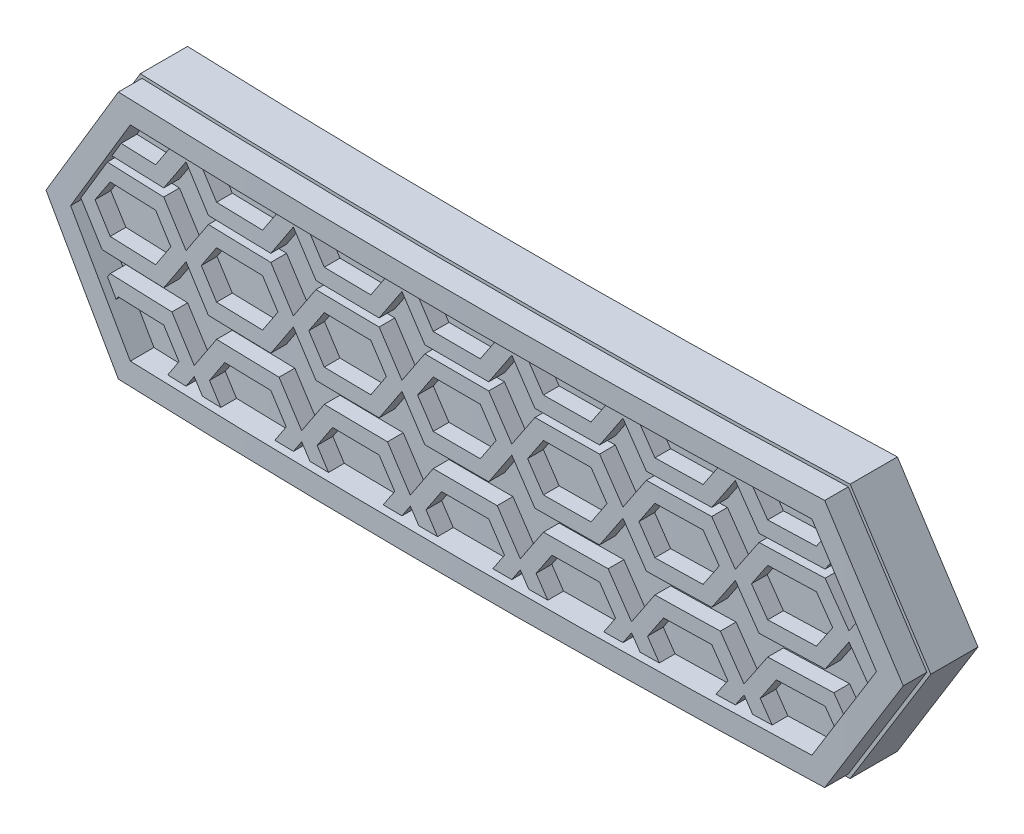
SolidWorks part; units mm, degrees
ref_plane "Front Plane" through (0, 0, 0) normal (0, 0, 1) x (1, 0, 0)
ref_plane "Top Plane" through (0, 0, 0) normal (0, 1, 0) x (1, 0, 0)
ref_plane "Right Plane" through (0, 0, 0) normal (1, 0, 0) x (0, 0, -1)
sketch "Sketch2" plane through (0, 0, 0) normal (0, 1, 0) x (1, 0, 0)
  line L3 (-73.1153, 2.6297) -> (-72.7519, 5.6076)
  line L4 (73.8847, 2.6297) -> (73.5213, 5.6076)
  arc A0 (-73.1153, 2.6297) -> (73.8847, 2.6297) centre (0.3847, 604.9793) ccw
  arc A1 (-72.7519, 5.6076) -> (73.5213, 5.6076) centre (0.3847, 604.9793) ccw
  dimension "D2" = 147
  dimension "D1" = 3
extrude "Boss-Extrude1" add sketch "Sketch2" along normal blind 25
sketch "Sketch3" plane through (0, 0, 0) normal (0, 0, 1) x (1, 0, 0)
  line L0 (0.3847, 25) -> (0, 0) construction
  line L1 (73.8847, 25) -> (-73.1153, 25) construction
  line L2 (-27.5937, 12.7392) -> (-22.6709, 20.843)
  line L3 (-22.6709, 20.843) -> (22.4834, 20.843)
  line L4 (-22.6709, 4.6354) -> (22.4834, 4.6354)
  line L5 (-27.5937, 12.7392) -> (-22.6709, 4.6354)
  line L6 (27.4063, 12.7392) -> (22.4834, 4.6354)
  line L7 (27.4063, 12.7392) -> (22.4834, 20.843)
  line L12 (-73.1153, 0) -> (73.8847, 0)
  line L13 (73.8847, 0) -> (73.8847, 25)
  line L14 (73.8847, 25) -> (-73.1153, 25)
  line L15 (-73.1153, 25) -> (-73.1153, 0)
  line L16 (-73.1153, 0) -> (73.8847, 0)
  line L17 (73.8847, 0) -> (73.8847, 25)
  line L18 (73.8847, 25) -> (-73.1153, 25)
  line L19 (-73.1153, 25) -> (-73.1153, 0)
  point P10 (-0.0937, 4.6354)
  point P12 (-0.0937, 20.843)
  dimension "D1" = 55
  dimension "D2" = 0
extrude "Cut-Extrude1" cut sketch "Sketch3" against normal through all both and the other way through all
sketch "Sketch4" plane through (0, 0, 0) normal (0, 0, 1) x (1, 0, 0)
  line L0 (-18.8894, 14.093) -> (-18.8894, 12.6877) construction
  line L1 (-25.6228, 13.0876) -> (-25.625, 13.0908)
  line L2 (8.1082, 6.1354) -> (9.31, 6.1354)
  line L3 (-17.4817, 6.1354) -> (-16.2798, 6.1354)
  line L4 (-12.8918, 6.1354) -> (-11.69, 6.1354)
  line L6 (-25.3906, 12.7392) -> (24.8112, 12.7392) construction
  line L7 (-18.8894, 23.6403) -> (-18.8894, 18.1877) construction
  line L10 (-10.4817, 6.1354) -> (-9.2798, 6.1354)
  line L11 (2.5774, 18.8928) -> (2.5774, 18.8879)
  line L12 (25.6512, 12.7392) -> (21.6395, 19.343)
  line L13 (21.6395, 19.343) -> (-21.827, 19.343)
  line L14 (-21.827, 19.343) -> (-25.8386, 12.7392)
  line L15 (-25.8386, 12.7392) -> (-21.827, 6.1354)
  line L16 (-21.827, 6.1354) -> (21.6395, 6.1354)
  line L17 (21.6395, 6.1354) -> (25.6512, 12.7392)
  line L18 (24.8368, 14.0798) -> (24.2638, 15.0231)
  line L19 (17.6789, 19.343) -> (16.4771, 19.343)
  line L20 (-23.0132, 17.3903) -> (-23.6207, 16.3903)
  line L21 (-23.8612, 9.4841) -> (-23.2882, 8.5408)
  line L22 (-19.8918, 6.1354) -> (-18.69, 6.1354)
  line L23 (22.6315, 7.7684) -> (23.2045, 8.7116)
  line L24 (-5.8918, 6.1354) -> (-4.69, 6.1354)
  line L25 (-3.4817, 6.1354) -> (-2.2798, 6.1354)
  line L26 (1.1082, 6.1354) -> (2.31, 6.1354)
  line L31 (10.5183, 6.1354) -> (11.7202, 6.1354)
  line L125 (-18.6228, 19.1931) -> (-18.7228, 19.343)
  line L126 (-20.0877, 16.3903) -> (-18.6228, 18.5876)
  line L127 (-20.0877, 16.3903) -> (-23.6207, 16.3903)
  line L130 (-20.6228, 17.3903) -> (-19.6228, 18.8903)
  line L131 (-19.6228, 18.8903) -> (-19.9246, 19.343)
  line L135 (-20.6228, 17.3903) -> (-23.0132, 17.3903)
  line L137 (-11.6228, 19.1931) -> (-11.7228, 19.343)
  line L138 (-13.0877, 16.3903) -> (-11.6228, 18.5876)
  line L139 (-13.0877, 16.3903) -> (-17.158, 16.3903)
  line L140 (-17.158, 16.3903) -> (-18.6228, 18.5876)
  line L141 (-18.6228, 19.1931) -> (-18.5229, 19.343)
  line L142 (-13.6228, 17.3903) -> (-12.6228, 18.8903)
  line L143 (-12.6228, 18.8903) -> (-12.9246, 19.343)
  line L145 (-17.6228, 18.8903) -> (-17.3211, 19.343)
  line L146 (-16.6228, 17.3903) -> (-17.6228, 18.8903)
  line L147 (-13.6228, 17.3903) -> (-16.6228, 17.3903)
  line L149 (-4.6228, 19.1931) -> (-4.7228, 19.343)
  line L150 (-6.0877, 16.3903) -> (-4.6228, 18.5876)
  line L151 (-6.0877, 16.3903) -> (-10.158, 16.3903)
  line L152 (-10.158, 16.3903) -> (-11.6228, 18.5876)
  line L153 (-11.6228, 19.1931) -> (-11.5229, 19.343)
  line L154 (-6.6228, 17.3903) -> (-5.6228, 18.8903)
  line L155 (-5.6228, 18.8903) -> (-5.9246, 19.343)
  line L157 (-10.6228, 18.8903) -> (-10.3211, 19.343)
  line L158 (-9.6228, 17.3903) -> (-10.6228, 18.8903)
  line L159 (-6.6228, 17.3903) -> (-9.6228, 17.3903)
  line L161 (2.579, 18.8903) -> (2.5774, 18.8928)
  line L162 (0.9123, 16.3903) -> (2.3772, 18.5876)
  line L163 (0.9123, 16.3903) -> (-3.158, 16.3903)
  line L164 (-3.158, 16.3903) -> (-4.6228, 18.5876)
  line L165 (-4.6228, 19.1931) -> (-4.5229, 19.343)
  line L166 (0.3772, 17.3903) -> (1.3772, 18.8903)
  line L167 (1.3772, 18.8903) -> (1.0754, 19.343)
  line L169 (-3.6228, 18.8903) -> (-3.3211, 19.343)
  line L170 (-2.6228, 17.3903) -> (-3.6228, 18.8903)
  line L171 (0.3772, 17.3903) -> (-2.6228, 17.3903)
  line L173 (9.3772, 19.1931) -> (9.2772, 19.343)
  line L174 (7.9123, 16.3903) -> (9.3772, 18.5876)
  line L175 (7.9123, 16.3903) -> (3.842, 16.3903)
  line L176 (3.842, 16.3903) -> (2.3772, 18.5876)
  line L177 (2.3772, 19.1931) -> (2.4771, 19.343)
  line L178 (7.3772, 17.3903) -> (8.3772, 18.8903)
  line L179 (8.3772, 18.8903) -> (8.0754, 19.343)
  line L181 (3.3772, 18.8903) -> (3.6789, 19.343)
  line L182 (4.3772, 17.3903) -> (3.3772, 18.8903)
  line L183 (7.3772, 17.3903) -> (4.3772, 17.3903)
  line L185 (16.3772, 19.1931) -> (16.2772, 19.343)
  line L186 (14.9123, 16.3903) -> (16.3772, 18.5876)
  line L187 (14.9123, 16.3903) -> (10.842, 16.3903)
  line L188 (10.842, 16.3903) -> (9.3772, 18.5876)
  line L189 (9.3772, 19.1931) -> (9.4771, 19.343)
  line L190 (14.3772, 17.3903) -> (15.3772, 18.8903)
  line L191 (15.3772, 18.8903) -> (15.0754, 19.343)
  line L193 (10.3772, 18.8903) -> (10.6789, 19.343)
  line L194 (11.3772, 17.3903) -> (10.3772, 18.8903)
  line L195 (14.3772, 17.3903) -> (11.3772, 17.3903)
  line L198 (21.9123, 16.3903) -> (22.7081, 17.584)
  line L199 (21.9123, 16.3903) -> (17.842, 16.3903)
  line L200 (17.842, 16.3903) -> (16.3772, 18.5876)
  line L201 (16.3772, 19.1931) -> (16.4771, 19.343)
  line L202 (21.3772, 17.3903) -> (22.1351, 18.5273)
  line L205 (17.3772, 18.8903) -> (17.6789, 19.343)
  line L206 (18.3772, 17.3903) -> (17.3772, 18.8903)
  line L207 (21.3772, 17.3903) -> (18.3772, 17.3903)
  line L244 (3.5183, 6.1354) -> (4.7202, 6.1354)
  line L245 (15.1082, 6.1354) -> (16.31, 6.1354)
  line L246 (17.5183, 6.1354) -> (18.7202, 6.1354)
  line L247 (24.6777, 11.1367) -> (25.2507, 12.08)
  line L248 (16.2772, 19.343) -> (15.0754, 19.343)
  line L249 (10.6789, 19.343) -> (9.4771, 19.343)
  line L339 (-25.6228, 13.0876) -> (-24.158, 10.8903)
  line L340 (-24.158, 10.8903) -> (-20.0877, 10.8903)
  line L341 (-18.6228, 13.0876) -> (-20.0877, 10.8903)
  line L342 (-20.0877, 15.8903) -> (-18.6228, 13.6931)
  line L343 (-20.0877, 15.8903) -> (-23.9244, 15.8903)
  line L345 (-20.6228, 14.8903) -> (-19.6228, 13.3903)
  line L346 (-19.6228, 13.3903) -> (-20.6228, 11.8903)
  line L347 (-23.6228, 11.8903) -> (-20.6228, 11.8903)
  line L348 (-24.6228, 13.3903) -> (-23.6228, 11.8903)
  line L349 (-23.6228, 14.8903) -> (-24.6228, 13.3903)
  line L350 (-20.6228, 14.8903) -> (-23.6228, 14.8903)
  line L351 (-18.6228, 13.0876) -> (-17.158, 10.8903)
  line L352 (-17.158, 10.8903) -> (-13.0877, 10.8903)
  line L353 (-11.6228, 13.0876) -> (-13.0877, 10.8903)
  line L354 (-13.0877, 15.8903) -> (-11.6228, 13.6931)
  line L355 (-13.0877, 15.8903) -> (-17.158, 15.8903)
  line L356 (-17.158, 15.8903) -> (-18.6228, 13.6931)
  line L357 (-13.6228, 14.8903) -> (-12.6228, 13.3903)
  line L358 (-12.6228, 13.3903) -> (-13.6228, 11.8903)
  line L359 (-16.6228, 11.8903) -> (-13.6228, 11.8903)
  line L360 (-17.6228, 13.3903) -> (-16.6228, 11.8903)
  line L361 (-16.6228, 14.8903) -> (-17.6228, 13.3903)
  line L362 (-13.6228, 14.8903) -> (-16.6228, 14.8903)
  line L363 (-11.6228, 13.0876) -> (-10.158, 10.8903)
  line L364 (-10.158, 10.8903) -> (-6.0877, 10.8903)
  line L365 (-4.6228, 13.0876) -> (-6.0877, 10.8903)
  line L366 (-6.0877, 15.8903) -> (-4.6228, 13.6931)
  line L367 (-6.0877, 15.8903) -> (-10.158, 15.8903)
  line L368 (-10.158, 15.8903) -> (-11.6228, 13.6931)
  line L369 (-6.6228, 14.8903) -> (-5.6228, 13.3903)
  line L370 (-5.6228, 13.3903) -> (-6.6228, 11.8903)
  line L371 (-9.6228, 11.8903) -> (-6.6228, 11.8903)
  line L372 (-10.6228, 13.3903) -> (-9.6228, 11.8903)
  line L373 (-9.6228, 14.8903) -> (-10.6228, 13.3903)
  line L374 (-6.6228, 14.8903) -> (-9.6228, 14.8903)
  line L375 (-4.6228, 13.0876) -> (-3.158, 10.8903)
  line L376 (-3.158, 10.8903) -> (0.9123, 10.8903)
  line L377 (0.9123, 15.8903) -> (2.3772, 13.6931)
  line L378 (0.9123, 15.8903) -> (-3.158, 15.8903)
  line L379 (-3.158, 15.8903) -> (-4.6228, 13.6931)
  line L380 (0.3772, 14.8903) -> (1.3772, 13.3903)
  line L381 (1.3772, 13.3903) -> (0.3772, 11.8903)
  line L382 (-2.6228, 11.8903) -> (0.3772, 11.8903)
  line L383 (-3.6228, 13.3903) -> (-2.6228, 11.8903)
  line L384 (-2.6228, 14.8903) -> (-3.6228, 13.3903)
  line L385 (0.3772, 14.8903) -> (-2.6228, 14.8903)
  line L386 (2.3772, 13.0876) -> (3.842, 10.8903)
  line L387 (3.842, 10.8903) -> (7.9123, 10.8903)
  line L388 (9.3772, 13.0876) -> (7.9123, 10.8903)
  line L389 (7.9123, 15.8903) -> (9.3772, 13.6931)
  line L390 (7.9123, 15.8903) -> (3.842, 15.8903)
  line L391 (3.842, 15.8903) -> (2.3772, 13.6931)
  line L392 (7.3772, 14.8903) -> (8.3772, 13.3903)
  line L393 (8.3772, 13.3903) -> (7.3772, 11.8903)
  line L394 (4.3772, 11.8903) -> (7.3772, 11.8903)
  line L395 (3.3772, 13.3903) -> (4.3772, 11.8903)
  line L396 (4.3772, 14.8903) -> (3.3772, 13.3903)
  line L397 (7.3772, 14.8903) -> (4.3772, 14.8903)
  line L398 (9.3772, 13.0876) -> (10.842, 10.8903)
  line L399 (10.842, 10.8903) -> (14.9123, 10.8903)
  line L400 (16.3772, 13.0876) -> (14.9123, 10.8903)
  line L401 (14.9123, 15.8903) -> (16.3772, 13.6931)
  line L402 (14.9123, 15.8903) -> (10.842, 15.8903)
  line L403 (10.842, 15.8903) -> (9.3772, 13.6931)
  line L404 (14.3772, 14.8903) -> (15.3772, 13.3903)
  line L405 (15.3772, 13.3903) -> (14.3772, 11.8903)
  line L406 (11.3772, 11.8903) -> (14.3772, 11.8903)
  line L407 (10.3772, 13.3903) -> (11.3772, 11.8903)
  line L408 (11.3772, 14.8903) -> (10.3772, 13.3903)
  line L409 (14.3772, 14.8903) -> (11.3772, 14.8903)
  line L410 (16.3772, 13.0876) -> (17.842, 10.8903)
  line L411 (17.842, 10.8903) -> (21.9123, 10.8903)
  line L412 (23.3772, 13.0876) -> (21.9123, 10.8903)
  line L413 (21.9123, 15.8903) -> (23.3772, 13.6931)
  line L414 (21.9123, 15.8903) -> (17.842, 15.8903)
  line L415 (17.842, 15.8903) -> (16.3772, 13.6931)
  line L416 (21.3772, 14.8903) -> (22.3772, 13.3903)
  line L417 (22.3772, 13.3903) -> (21.3772, 11.8903)
  line L418 (18.3772, 11.8903) -> (21.3772, 11.8903)
  line L419 (17.3772, 13.3903) -> (18.3772, 11.8903)
  line L420 (18.3772, 14.8903) -> (17.3772, 13.3903)
  line L421 (21.3772, 14.8903) -> (18.3772, 14.8903)
  line L422 (23.3772, 13.0876) -> (24.6777, 11.1367)
  line L427 (24.2638, 15.0231) -> (23.3772, 13.6931)
  line L431 (24.3772, 13.3903) -> (25.2507, 12.08)
  line L432 (24.8368, 14.0798) -> (24.3772, 13.3903)
  line L451 (9.2772, 19.343) -> (8.0754, 19.343)
  line L452 (2.2772, 19.343) -> (1.0754, 19.343)
  line L453 (-4.7228, 19.343) -> (-5.9246, 19.343)
  line L454 (-11.7228, 19.343) -> (-12.9246, 19.343)
  line L455 (-18.7228, 19.343) -> (-19.9246, 19.343)
  line L456 (2.3772, 19.1931) -> (2.2772, 19.343)
  line L457 (2.5774, 18.8879) -> (2.579, 18.8903)
  line L460 (2.3772, 13.0876) -> (0.9123, 10.8903)
  line L461 (2.5774, 13.3928) -> (2.5774, 13.3879)
  line L462 (2.5774, 13.3928) -> (2.579, 13.3903)
  line L463 (22.7081, 17.584) -> (22.1351, 18.5273)
  line L464 (-17.3211, 19.343) -> (-18.5229, 19.343)
  line L465 (-23.9244, 15.8903) -> (-25.625, 13.0908)
  line L467 (-10.3211, 19.343) -> (-11.5229, 19.343)
  line L468 (-18.3524, 8.047) -> (-18.3524, 6.6418) construction
  line L471 (-3.3211, 19.343) -> (-4.5229, 19.343)
  line L472 (3.1144, 7.3469) -> (3.1144, 7.342)
  line L473 (3.6789, 19.343) -> (2.4771, 19.343)
  line L573 (-23.621, 9.8444) -> (-19.5506, 9.8444)
  line L574 (-18.0858, 7.6472) -> (-19.5506, 9.8444)
  line L575 (-18.69, 6.1354) -> (-18.0858, 7.0416)
  line L578 (-23.8612, 9.4841) -> (-23.621, 9.8444)
  line L579 (-19.8918, 6.1354) -> (-19.0858, 7.3444)
  line L580 (-19.0858, 7.3444) -> (-20.0858, 8.8444)
  line L581 (-23.0858, 8.8444) -> (-20.0858, 8.8444)
  line L582 (-23.2882, 8.5408) -> (-23.0858, 8.8444)
  line L585 (-16.621, 9.8444) -> (-12.5506, 9.8444)
  line L586 (-11.0858, 7.6472) -> (-12.5506, 9.8444)
  line L587 (-11.69, 6.1354) -> (-11.0858, 7.0416)
  line L589 (-17.4817, 6.1354) -> (-18.0858, 7.0416)
  line L590 (-18.0858, 7.6472) -> (-16.621, 9.8444)
  line L591 (-12.8918, 6.1354) -> (-12.0858, 7.3444)
  line L592 (-12.0858, 7.3444) -> (-13.0858, 8.8444)
  line L593 (-16.0858, 8.8444) -> (-13.0858, 8.8444)
  line L594 (-17.0858, 7.3444) -> (-16.0858, 8.8444)
  line L595 (-16.2798, 6.1354) -> (-17.0858, 7.3444)
  line L597 (-9.621, 9.8444) -> (-5.5506, 9.8444)
  line L598 (-4.0858, 7.6472) -> (-5.5506, 9.8444)
  line L599 (-4.69, 6.1354) -> (-4.0858, 7.0416)
  line L601 (-10.4817, 6.1354) -> (-11.0858, 7.0416)
  line L602 (-11.0858, 7.6472) -> (-9.621, 9.8444)
  line L603 (-5.8918, 6.1354) -> (-5.0858, 7.3444)
  line L604 (-5.0858, 7.3444) -> (-6.0858, 8.8444)
  line L605 (-9.0858, 8.8444) -> (-6.0858, 8.8444)
  line L606 (-10.0858, 7.3444) -> (-9.0858, 8.8444)
  line L607 (-9.2798, 6.1354) -> (-10.0858, 7.3444)
  line L609 (-2.621, 9.8444) -> (1.4494, 9.8444)
  line L610 (3.116, 7.3444) -> (3.1144, 7.3469)
  line L611 (2.31, 6.1354) -> (2.9142, 7.0416)
  line L613 (-3.4817, 6.1354) -> (-4.0858, 7.0416)
  line L614 (-4.0858, 7.6472) -> (-2.621, 9.8444)
  line L615 (1.1082, 6.1354) -> (1.9142, 7.3444)
  line L616 (1.9142, 7.3444) -> (0.9142, 8.8444)
  line L617 (-2.0858, 8.8444) -> (0.9142, 8.8444)
  line L618 (-3.0858, 7.3444) -> (-2.0858, 8.8444)
  line L619 (-2.2798, 6.1354) -> (-3.0858, 7.3444)
  line L621 (4.379, 9.8444) -> (8.4494, 9.8444)
  line L622 (9.9142, 7.6472) -> (8.4494, 9.8444)
  line L623 (9.31, 6.1354) -> (9.9142, 7.0416)
  line L625 (3.5183, 6.1354) -> (2.9142, 7.0416)
  line L626 (2.9142, 7.6472) -> (4.379, 9.8444)
  line L627 (8.1082, 6.1354) -> (8.9142, 7.3444)
  line L628 (8.9142, 7.3444) -> (7.9142, 8.8444)
  line L629 (4.9142, 8.8444) -> (7.9142, 8.8444)
  line L630 (3.9142, 7.3444) -> (4.9142, 8.8444)
  line L631 (4.7202, 6.1354) -> (3.9142, 7.3444)
  line L633 (11.379, 9.8444) -> (15.4494, 9.8444)
  line L634 (16.9142, 7.6472) -> (15.4494, 9.8444)
  line L635 (16.31, 6.1354) -> (16.9142, 7.0416)
  line L637 (10.5183, 6.1354) -> (9.9142, 7.0416)
  line L638 (9.9142, 7.6472) -> (11.379, 9.8444)
  line L639 (15.1082, 6.1354) -> (15.9142, 7.3444)
  line L640 (15.9142, 7.3444) -> (14.9142, 8.8444)
  line L641 (11.9142, 8.8444) -> (14.9142, 8.8444)
  line L642 (10.9142, 7.3444) -> (11.9142, 8.8444)
  line L643 (11.7202, 6.1354) -> (10.9142, 7.3444)
  line L645 (18.379, 9.8444) -> (22.4494, 9.8444)
  line L646 (23.2045, 8.7116) -> (22.4494, 9.8444)
  line L649 (17.5183, 6.1354) -> (16.9142, 7.0416)
  line L650 (16.9142, 7.6472) -> (18.379, 9.8444)
  line L652 (22.6315, 7.7684) -> (21.9142, 8.8444)
  line L653 (18.9142, 8.8444) -> (21.9142, 8.8444)
  line L654 (17.9142, 7.3444) -> (18.9142, 8.8444)
  line L655 (18.7202, 6.1354) -> (17.9142, 7.3444)
  line L905 (2.9142, 7.6472) -> (1.4494, 9.8444)
  line L906 (3.1144, 7.342) -> (3.116, 7.3444)
  dimension "D1" = 1.5
extrude "Boss-Extrude2" add sketch "Sketch4" along normal blind 10
sketch "Sketch5" plane through (0, 20.843, 0) normal (0, 1, 0) x (1, 0, 0)
  line L2 (-27.6398, -2.1916) -> (-28.0434, -10.9342)
  line L3 (-28.0434, -10.9342) -> (27.4508, -11.6874)
  line L4 (27.4508, -11.6874) -> (27.4508, -2.2351)
  arc A6 (-27.6398, -2.1916) -> (-22.7088, -2.3992) centre (0.3847, 604.9793) ccw
  arc A7 (-22.7088, -2.3992) -> (22.5198, -2.4349) centre (0.3847, 604.9793) ccw
  arc A8 (22.5198, -2.4349) -> (27.4508, -2.2351) centre (0.3847, 604.9793) ccw
extrude "Cut-Extrude2" cut sketch "Sketch5" against normal through all
sketch "Sketch6" plane through (0, 0, 0) normal (0, 0, 1) x (1, 0, 0)
  line L21 (-21.7707, 19.243) -> (-25.7216, 12.7392)
  line L22 (-25.7216, 12.7392) -> (-21.7707, 6.2354)
  line L23 (-21.7707, 6.2354) -> (21.5833, 6.2354)
  line L24 (21.5833, 6.2354) -> (25.5342, 12.7392)
  line L25 (25.5342, 12.7392) -> (21.5833, 19.243)
  line L26 (21.5833, 19.243) -> (-21.7707, 19.243)
  line L27 (27.1723, 12.7392) -> (22.3709, 20.643)
  line L28 (22.3709, 4.8354) -> (27.1723, 12.7392)
  line L29 (-22.5583, 4.8354) -> (22.3709, 4.8354)
  line L30 (-27.3597, 12.7392) -> (-22.5583, 4.8354)
  line L31 (-22.5583, 20.643) -> (-27.3597, 12.7392)
  line L32 (22.3709, 20.643) -> (-22.5583, 20.643)
  line L33 (27.1723, 12.7392) -> (22.3709, 20.643)
  line L34 (22.3709, 4.8354) -> (27.1723, 12.7392)
  line L35 (-22.5583, 4.8354) -> (22.3709, 4.8354)
  line L36 (-27.3597, 12.7392) -> (-22.5583, 4.8354)
  line L37 (-22.5583, 20.643) -> (-27.3597, 12.7392)
  line L38 (22.3709, 20.643) -> (-22.5583, 20.643)
  dimension "D1" = 0.2
  dimension "D2" = 1.4
extrude "Boss-Extrude3" add sketch "Sketch6" along normal blind 10
sketch "Sketch7" plane through (0, 20.843, 0) normal (0, 1, 0) x (1, 0, 0)
  line L2 (-27.6629, -2.6911) -> (-27.6629, -11.5419)
  line L3 (-27.6629, -11.5419) -> (28.3478, -11.5419)
  line L4 (28.3478, -11.5419) -> (27.4731, -2.7346)
  arc A11 (-27.6629, -2.6911) -> (-22.7278, -2.8988) centre (0.3847, 604.9793) ccw
  arc A12 (-22.7278, -2.8988) -> (22.538, -2.9345) centre (0.3847, 604.9793) ccw
  arc A13 (22.538, -2.9345) -> (27.4731, -2.7346) centre (0.3847, 604.9793) ccw
extrude "Cut-Extrude3" cut sketch "Sketch7" against normal blind 20
